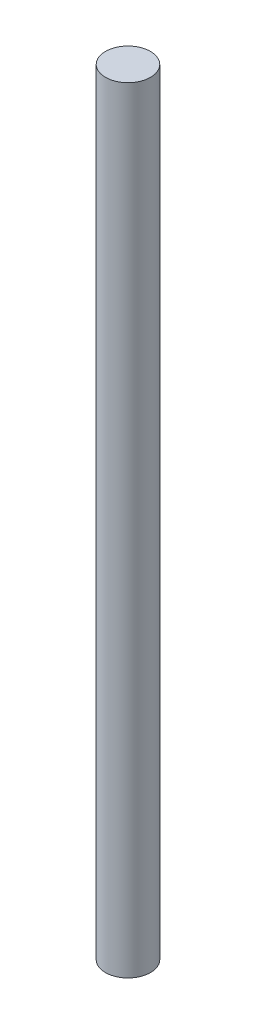
SolidWorks part; units mm, degrees
material "policarbonato"
ref_plane "Alzado" through (0, 0, 0) normal (0, 0, 1) x (1, 0, 0)
ref_plane "Planta" through (0, 0, 0) normal (0, 1, 0) x (1, 0, 0)
ref_plane "Vista lateral" through (0, 0, 0) normal (1, 0, 0) x (0, 0, -1)
sketch "Croquis1" plane through (0, 0, 0) normal (0, 1, 0) x (1, 0, 0)
  circle A0 centre (0, 0) radius 1.45
  dimension "D1" = 2.9
extrude "Saliente-Extruir1" add sketch "Croquis1" along normal blind 50
